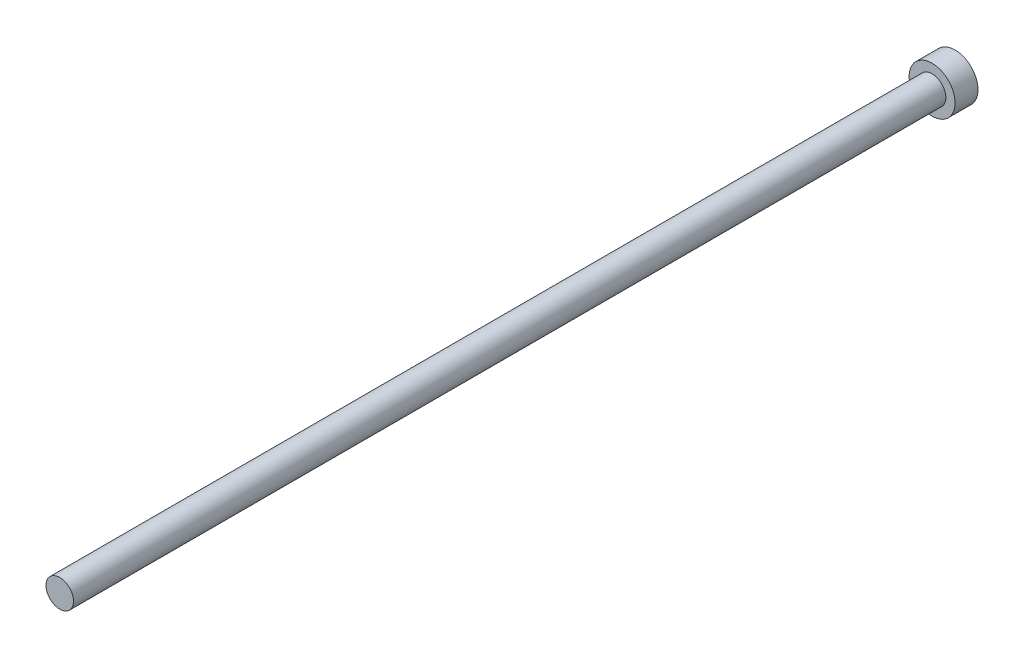
SolidWorks part; units mm, degrees
ref_plane "Front Plane" through (0, 0, 0) normal (0, 0, 1) x (1, 0, 0)
ref_plane "Top Plane" through (0, 0, 0) normal (0, 1, 0) x (1, 0, 0)
ref_plane "Right Plane" through (0, 0, 0) normal (1, 0, 0) x (0, 0, -1)
sketch "Sketch2" plane through (0, 0, 0) normal (0, 0, 1) x (1, 0, 0)
  circle A0 centre (0, 0) radius 5
  dimension "D1" = 10
extrude "Boss-Extrude2" add sketch "Sketch2" along normal blind 5 contours A0
sketch "Sketch5" plane through (0, 0, 0) normal (0, 0, -1) x (-1, 0, 0)
  line L1 (-3.2291, 1.899) -> (-3.2591, -1.847)
  line L2 (-3.2591, -1.847) -> (-0.03, -3.746)
  line L3 (-0.03, -3.746) -> (3.2291, -1.899)
  line L4 (3.2291, -1.899) -> (3.2591, 1.847)
  line L5 (3.2591, 1.847) -> (0.03, 3.746)
  line L6 (0.03, 3.746) -> (-3.2291, 1.899)
  circle A0 centre (0, 0) radius 3.2442 construction
extrude "Cut-Extrude2" cut sketch "Sketch5" against normal blind 3
sketch "Sketch6" plane through (0, 0, 5) normal (0, 0, 1) x (1, 0, 0)
  circle A0 centre (0, 0) radius 3
extrude "Boss-Extrude3" add sketch "Sketch6" along normal blind 190
